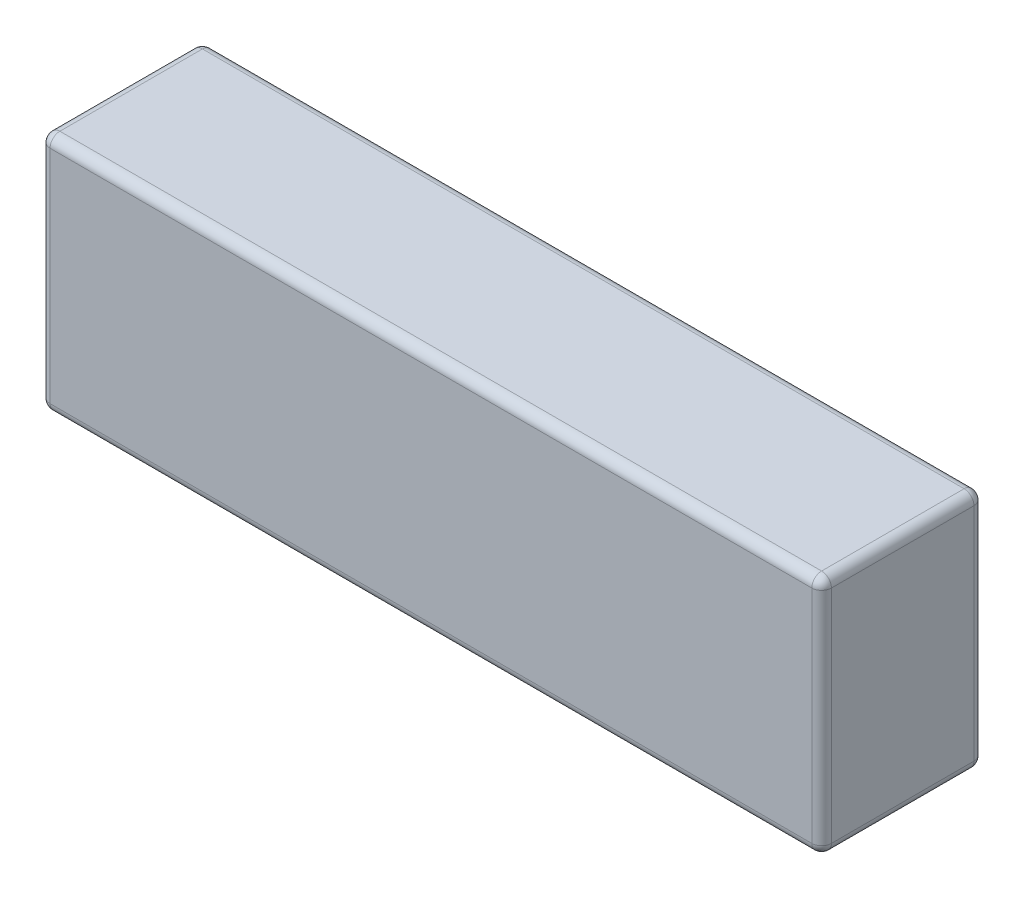
SolidWorks part; units mm, degrees
ref_plane "Front Plane" through (0, 0, 0) normal (0, 0, 1) x (1, 0, 0)
ref_plane "Top Plane" through (0, 0, 0) normal (0, 1, 0) x (1, 0, 0)
ref_plane "Right Plane" through (0, 0, 0) normal (1, 0, 0) x (0, 0, -1)
sketch "Sketch1" plane through (0, 0, 0) normal (0, 1, 0) x (1, 0, 0)
  line L1 (0, 0) -> (159, 0)
  line L2 (0, 0) -> (0, 33)
  line L3 (0, 33) -> (159, 33)
  line L4 (159, 0) -> (159, 33)
  dimension "D1" = 159
  dimension "D2" = 33
extrude "Boss-Extrude1" add sketch "Sketch1" along normal blind 49
fillet "Fillet1" radius 2 12 edges at (0, 24.5, 0) (159, 24.5, 0) (79.5, 0, 0) (159, 0, -16.5) (0, 0, -16.5) (159, 49, -16.5) (79.5, 49, 0) (0, 49, -16.5) (159, 24.5, -33) (79.5, 49, -33) (0, 24.5, -33) (79.5, 0, -33)
